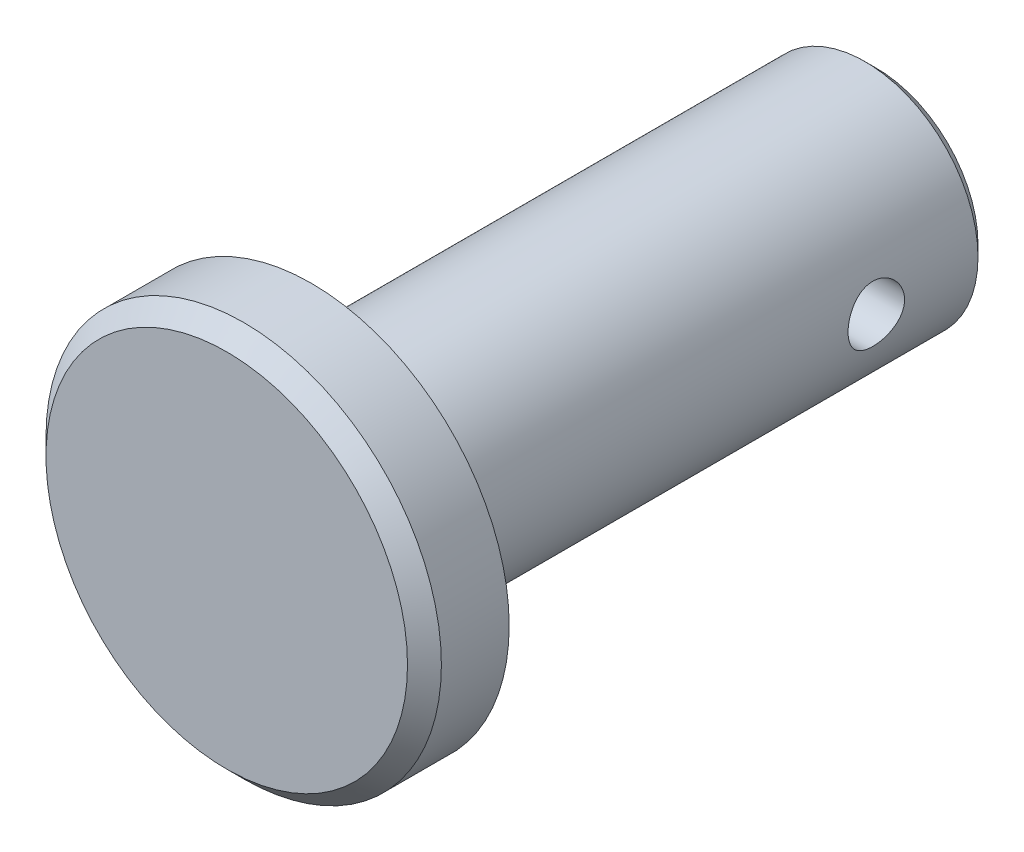
SolidWorks part; units mm, degrees
ref_plane "Front" through (0, 0, 0) normal (0, 0, 1) x (1, 0, 0)
ref_plane "Top" through (0, 0, 0) normal (0, 1, 0) x (1, 0, 0)
ref_plane "Right" through (0, 0, 0) normal (1, 0, 0) x (0, 0, -1)
sketch "Sketch1" plane through (0, 0, 0) normal (0, 0, 1) x (1, 0, 0)
  circle A0 centre (0, 0) radius 4
  point P3 (0, 4)
  point P4 (0, -4)
  dimension "dia" = 8
extrude "Extrude1" add sketch "Sketch1" along normal mid plane 20
sketch "Sketch2" plane through (0, 0, 10) normal (0, 0, 1) x (1, 0, 0)
  circle A0 centre (0, 0) radius 7
  dimension "head dia" = 14
extrude "Extrude2" add sketch "Sketch2" along normal blind 3
chamfer "Chamfer1" distance 0.6 angle 45 1 edges at (7, 0, 13)
sketch "Sketch3" plane through (0, 0, 0) normal (1, 0, 0) x (0, 0, -1)
  line L0 (-10, -4) -> (-10, 4) construction
  circle A0 centre (6, 0) radius 1
  point P2 (5, 0)
  dimension "hole dia" = 2
  dimension "useable Lg" = 15
extrude "Extrude3" cut sketch "Sketch3" against normal through all and the other way through all
chamfer "Chamfer2" distance 0.4 angle 45 1 edges at (4, 0, -10)
ref_plane "Plane1" through (0, 0, -6) normal (0, 0, 1) x (1, 0, 0)
sketch "Sketch8" plane through (0, 0, 0) normal (1, 0, 0) x (0, 0, -1)
  line L0 (-13, 6.4) -> (-13, -6.4) construction
  line L1 (-12.4, -7) -> (-10, -7) construction
  line L2 (10, -3.6) -> (10, 3.6) construction
  point P0 (-13, 7)
  point P1 (-10, 7)
  point P5 (10, 4)
  point P8 (-13, -7)
  point P9 (10, -4)
equation "\"D1@Chamfer1\" = \"head ht@Extrude2\" * .2"
equation "\"D1@Chamfer2\" = \"dia@Sketch1\" * .05"
